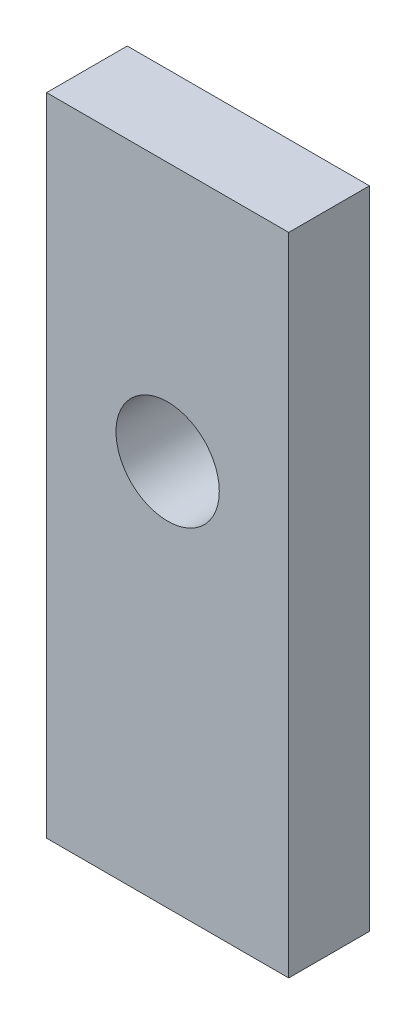
SolidWorks part; units mm, degrees
ref_plane "Front Plane" through (0, 0, 0) normal (0, 0, 1) x (1, 0, 0)
ref_plane "Top Plane" through (0, 0, 0) normal (0, 1, 0) x (1, 0, 0)
ref_plane "Right Plane" through (0, 0, 0) normal (1, 0, 0) x (0, 0, -1)
sketch "Sketch1" plane through (0, 0, 0) normal (0, 0, 1) x (1, 0, 0)
  line L0 (0, 20) -> (0, 3.9595) construction
  line L1 (-7.5, -20) -> (7.5, -20)
  line L2 (-7.5, -20) -> (-7.5, 20)
  line L3 (-7.5, 20) -> (7.5, 20)
  line L4 (7.5, -20) -> (7.5, 20)
  line L5 (-7.5, -20) -> (7.5, 20) construction
  line L6 (-7.5, 20) -> (7.5, -20) construction
  circle A1 centre (0, 3.9595) radius 3.2
  point P0 (0, 0)
  dimension "D2" = 6.4
  dimension "D1" = 40
  dimension "D3" = 15
  dimension "D4" = 23.9595
extrude "Boss-Extrude1" add sketch "Sketch1" along normal mid plane 5 contours L3 L4 L1 L2 | A1
